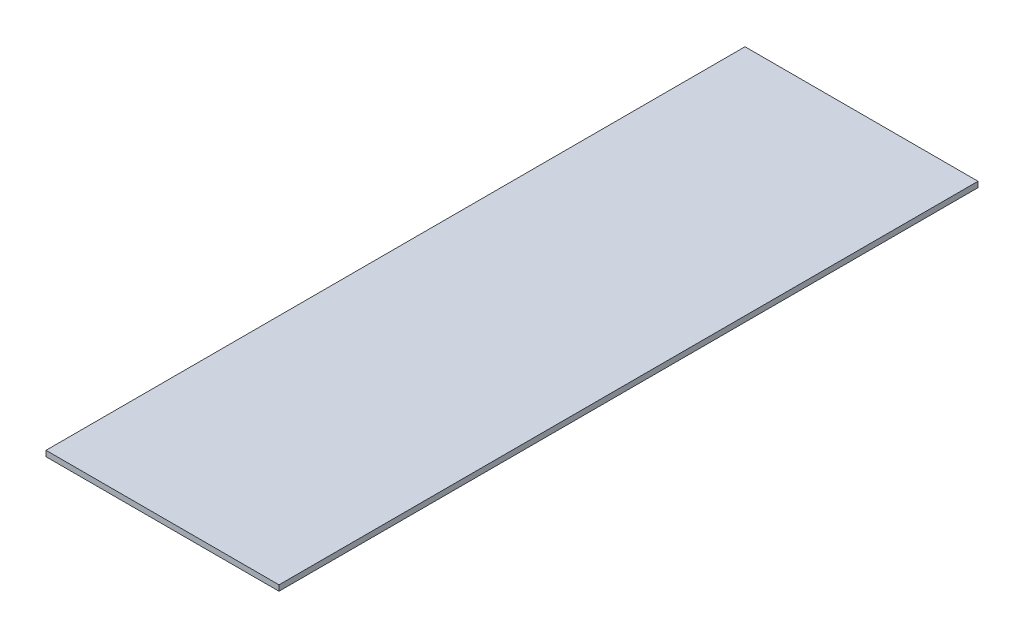
SolidWorks part; units mm, degrees
material "混凝土"
ref_plane "前视基准面" through (0, 0, 0) normal (0, 0, 1) x (1, 0, 0)
ref_plane "上视基准面" through (0, 0, 0) normal (0, 1, 0) x (1, 0, 0)
ref_plane "右视基准面" through (0, 0, 0) normal (1, 0, 0) x (0, 0, -1)
sketch "草图1" plane through (0, 0, 0) normal (0, 1, 0) x (1, 0, 0)
  line L0 (-2500, 7500) -> (2500, -7500) construction
  line L1 (2500, -7500) -> (-2500, -7500)
  line L2 (2500, -7500) -> (2500, 7500)
  line L3 (2500, 7500) -> (-2500, 7500)
  line L4 (-2500, -7500) -> (-2500, 7500)
  line L5 (-2500, -7500) -> (2500, 7500) construction
  dimension "D1" = 5000
  dimension "D2" = 15000
extrude "凸台-拉伸1" add sketch "草图1" against normal blind 120
